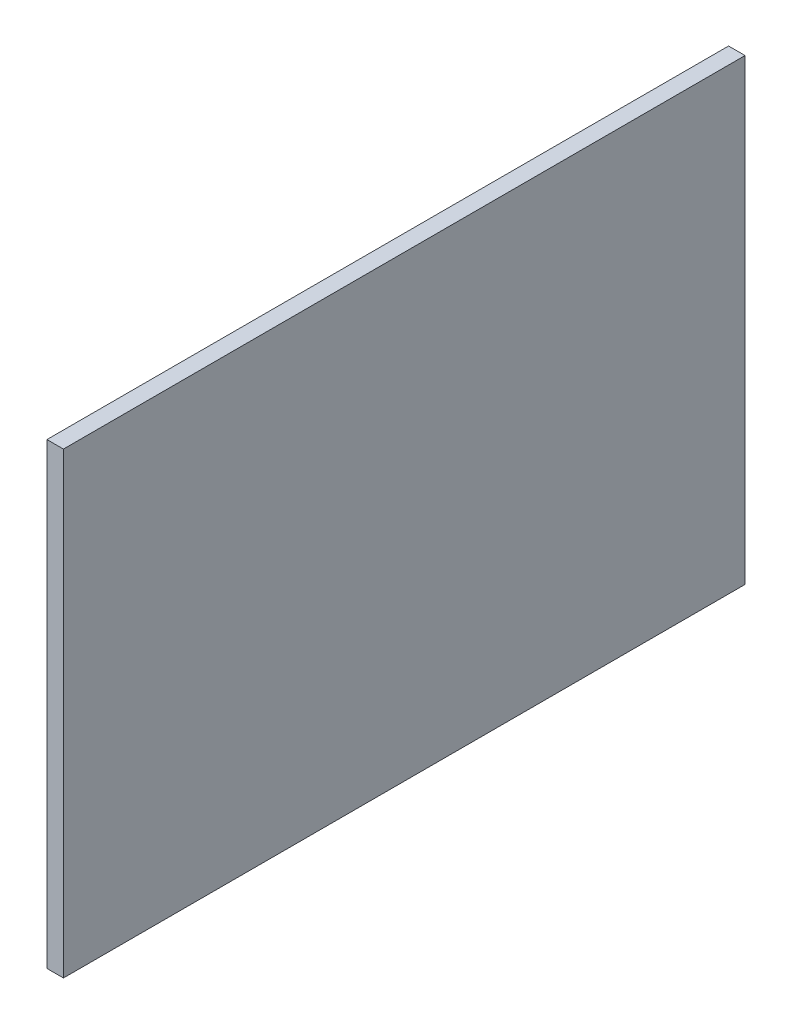
SolidWorks part; units mm, degrees
ref_plane "Front Plane" through (0, 0, 0) normal (0, 0, 1) x (1, 0, 0)
ref_plane "Top Plane" through (0, 0, 0) normal (0, 1, 0) x (1, 0, 0)
ref_plane "Right Plane" through (0, 0, 0) normal (1, 0, 0) x (0, 0, -1)
sketch "Sketch1" plane through (0, 0, 0) normal (1, 0, 0) x (0, 0, -1)
  line L1 (-74.0535, -465.925) -> (669.9465, -465.925)
  line L2 (-74.0535, -465.925) -> (-74.0535, 34.075)
  line L3 (-74.0535, 34.075) -> (669.9465, 34.075)
  line L4 (669.9465, -465.925) -> (669.9465, 34.075)
  line L5 (-74.0535, -465.925) -> (669.9465, 34.075) construction
  line L6 (-74.0535, 34.075) -> (669.9465, -465.925) construction
  point P0 (297.9465, -215.925)
  dimension "D1" = 744
  dimension "D2" = 500
extrude "Boss-Extrude1" add sketch "Sketch1" along normal blind 18
